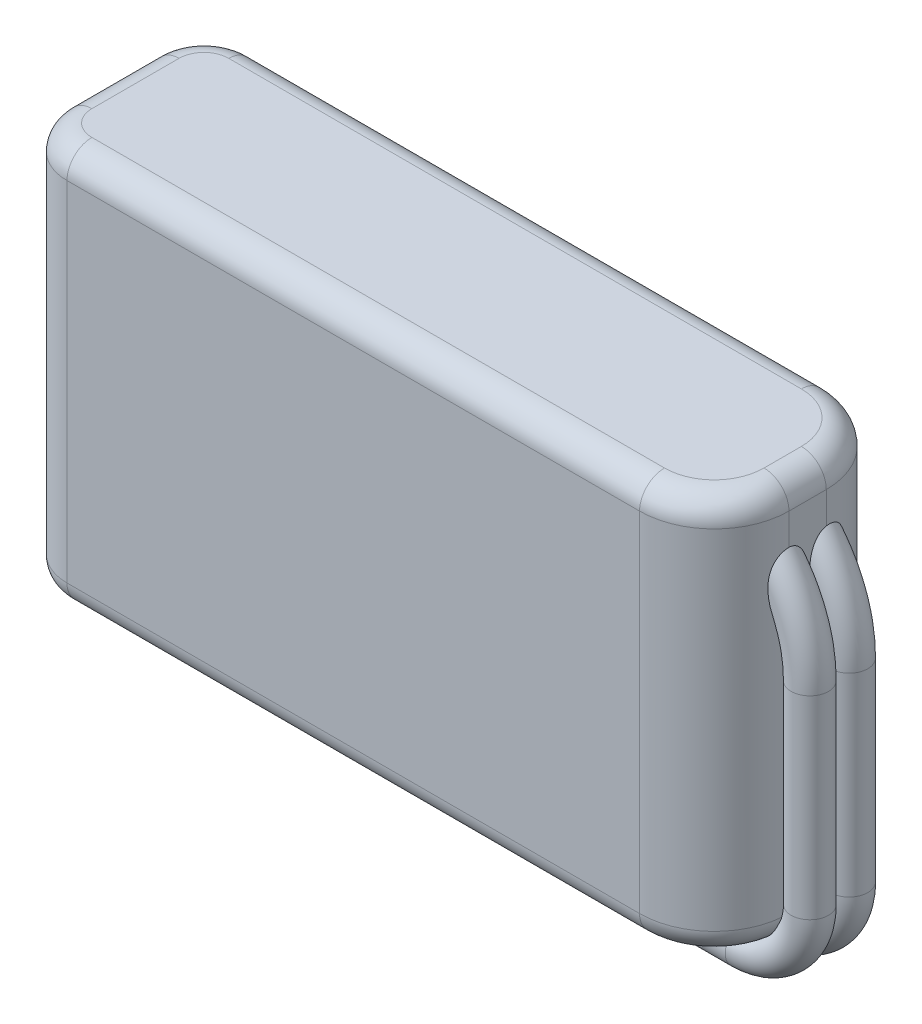
SolidWorks part; units mm, degrees
ref_plane "Front Plane" through (0, 0, 0) normal (0, 0, 1) x (1, 0, 0)
ref_plane "Top Plane" through (0, 0, 0) normal (0, 1, 0) x (1, 0, 0)
ref_plane "Right Plane" through (0, 0, 0) normal (1, 0, 0) x (0, 0, -1)
sketch "Sketch1" plane through (0, 0, 0) normal (0, 1, 0) x (1, 0, 0)
  line L1 (-28, -7.5) -> (28, -7.5)
  line L2 (-28, -7.5) -> (-28, 7.5)
  line L3 (-28, 7.5) -> (28, 7.5)
  line L4 (28, -7.5) -> (28, 7.5)
  line L5 (-28, -7.5) -> (28, 7.5) construction
  line L6 (-28, 7.5) -> (28, -7.5) construction
  point P0 (0, 0)
  dimension "D1" = 15
  dimension "D2" = 56
extrude "Boss-Extrude1" add sketch "Sketch1" along normal blind 32
fillet "Fillet1" radius 4 2 edges at (-28, 16, -7.5) (-28, 16, 7.5)
fillet "Fillet2" radius 6 2 edges at (28, 16, -7.5) (28, 16, 7.5)
fillet "Fillet3" radius 2 16 edges at (-26.8284, 0, 6.3284) (-28, 0, 0) (-26.8284, 0, -6.3284) (-1, 0, -7.5) (26.2426, 0, -5.7426) (28, 0, 0) (26.2426, 0, 5.7426) (-26.8284, 32, 6.3284) (-28, 32, 0) (-26.8284, 32, -6.3284) (-1, 32, -7.5) (26.2426, 32, -5.7426) (28, 32, 0) (26.2426, 32, 5.7426) (-1, 0, 7.5) (-1, 32, 7.5)
sketch "Sketch3" plane through (0, 0, -7.5) normal (0, 0, -1) x (-1, 0, 0)
  line L0 (0.1399, -2.5236) -> (-24.3809, -2.5236)
  line L1 (-30.3704, 3.4659) -> (-30.3704, 19.0429)
  line L2 (-22, 30) -> (-28, 30) construction
  arc A0 (-24.3809, -2.5236) -> (-30.3704, 3.4659) centre (-24.3809, 3.4659) cw
  arc A1 (-30.3704, 19.0429) -> (-23.2209, 30) centre (-18.3994, 19.0429) cw
sketch "Sketch4" plane through (0, 0, 0) normal (1, 0, 0) x (0, 0, -1)
  circle A0 centre (1.6566, -1.8315) radius 1.5
  circle A1 centre (-1.5, -1.8315) radius 1.5
  dimension "D1" = 3
  dimension "D2" = 1.5
sweep "Sweep2" add profiles "Sketch4" path "Sketch3"
